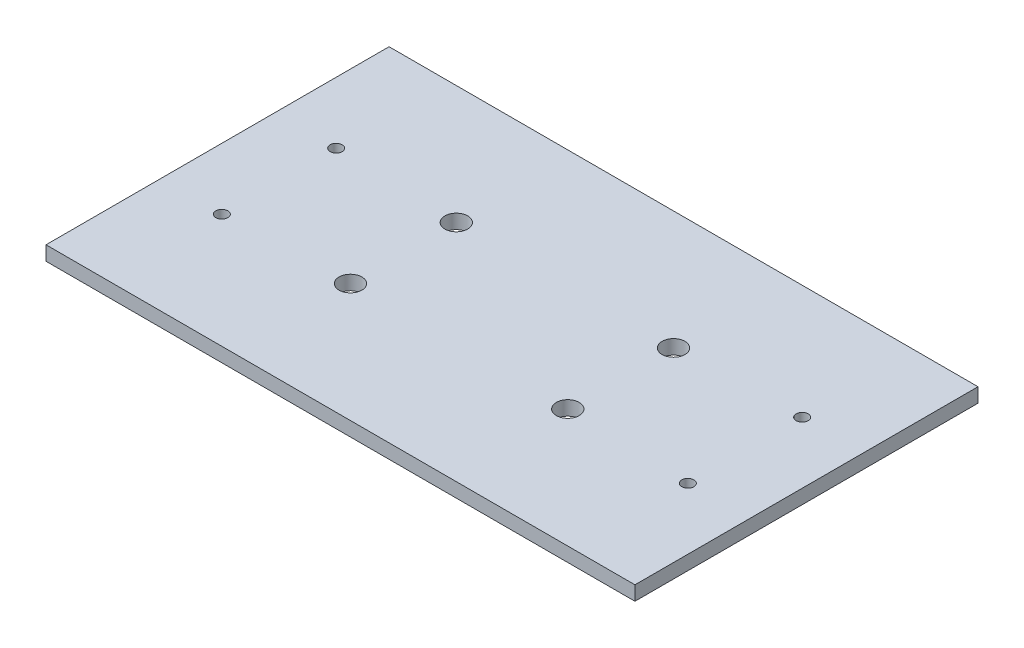
SolidWorks part; units mm, degrees
ref_plane "前视基准面" through (0, 0, 0) normal (0, 0, 1) x (1, 0, 0)
ref_plane "上视基准面" through (0, 0, 0) normal (0, 1, 0) x (1, 0, 0)
ref_plane "右视基准面" through (0, 0, 0) normal (1, 0, 0) x (0, 0, -1)
sketch "草图1" plane through (0, 0, 0) normal (0, 1, 0) x (1, 0, 0)
  line L1 (-103, -60) -> (103, -60)
  line L2 (-103, -60) -> (-103, 60)
  line L3 (-103, 60) -> (103, 60)
  line L4 (103, -60) -> (103, 60)
  line L5 (-103, -60) -> (103, 60) construction
  line L6 (-103, 60) -> (103, -60) construction
  point P0 (0, 0)
  dimension "D1" = 120
  dimension "D2" = 206
extrude "凸台-拉伸1" add sketch "草图1" along normal blind 5
sketch "草图2" plane through (0, 5, 0) normal (0, 1, 0) x (1, 0, 0)
  line L0 (0, -91.8916) -> (0, 91.8916) construction
  line L1 (-143.9998, 0) -> (143.9998, 0) construction
  line L2 (-103, 60) -> (-103, -60) construction
  circle A0 centre (-81.5, 20) radius 2.1
  circle A1 centre (81.5, 20) radius 2.1
  circle A2 centre (81.5, -20) radius 2.1
  circle A3 centre (-81.5, -20) radius 2.1
  point P4 (0, 0)
  point P8 (0, 0)
  dimension "D1" = 4.2
  dimension "D2" = 21.5
  dimension "D3" = 40
extrude "切除-拉伸1" cut sketch "草图2" against normal through all
sketch "草图3" plane through (0, 5, 0) normal (0, 1, 0) x (1, 0, 0)
  line L0 (-174.119, 0) -> (174.119, 0) construction
  line L1 (0, 135.391) -> (0, -135.391) construction
  circle A0 centre (-38, 18.5) radius 4
  circle A1 centre (38, 18.5) radius 4
  circle A2 centre (38, -18.5) radius 4
  circle A3 centre (-38, -18.5) radius 4
  point P4 (0, 0)
  point P8 (0, 0)
  dimension "D1" = 76
  dimension "D2" = 37
extrude "切除-拉伸2" cut sketch "草图3" against normal through all
